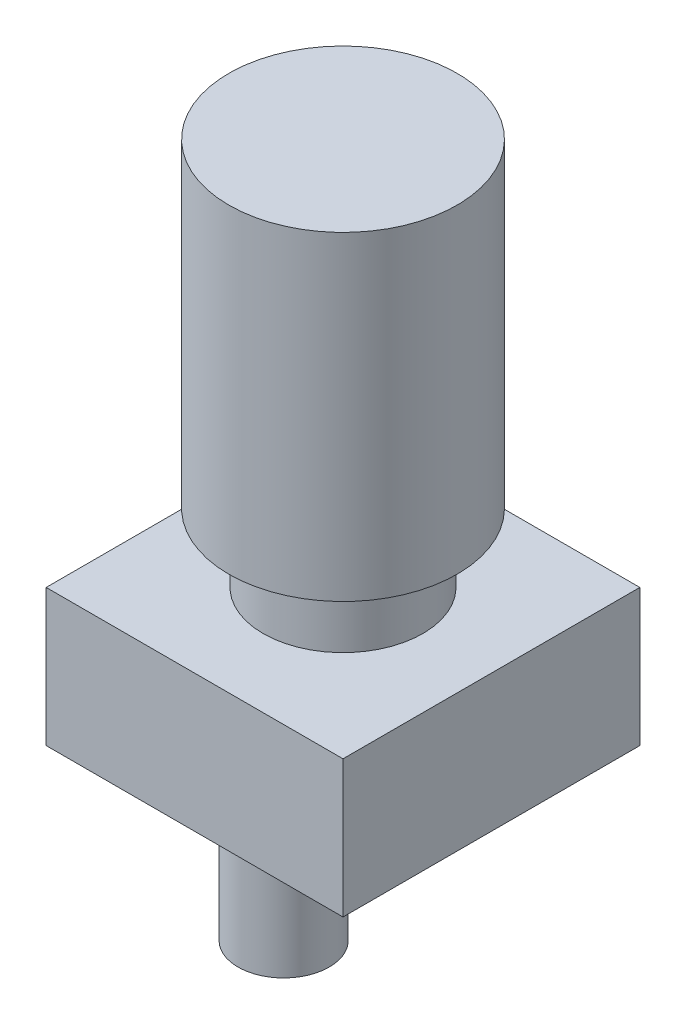
SolidWorks part; units mm, degrees
ref_plane "Front Plane" through (0, 0, 0) normal (0, 0, 1) x (1, 0, 0)
ref_plane "Top Plane" through (0, 0, 0) normal (0, 1, 0) x (1, 0, 0)
ref_plane "Right Plane" through (0, 0, 0) normal (1, 0, 0) x (0, 0, -1)
sketch "Sketch1" plane through (0, 0, 0) normal (0, 1, 0) x (1, 0, 0)
  line L0 (32.5, 32.5) -> (-32.5, -32.5) construction
  line L1 (-32.5, 32.5) -> (32.5, 32.5)
  line L2 (-32.5, 32.5) -> (-32.5, -32.5)
  line L3 (-32.5, -32.5) -> (32.5, -32.5)
  line L4 (32.5, 32.5) -> (32.5, -32.5)
  line L5 (-32.5, 32.5) -> (32.5, -32.5) construction
  dimension "D1" = 65
extrude "Boss-Extrude1" add sketch "Sketch1" along normal blind 30
sketch "Sketch3" plane through (0, 30, 0) normal (0, 1, 0) x (1, 0, 0)
  circle A0 centre (0, 0) radius 17.5
extrude "Boss-Extrude2" add sketch "Sketch3" along normal blind 15
sketch "Sketch4" plane through (0, 45, 0) normal (0, 1, 0) x (1, 0, 0)
  circle A0 centre (0, 0) radius 25
extrude "Boss-Extrude3" add sketch "Sketch4" along normal blind 70
sketch "Sketch5" plane through (0, 0, 0) normal (0, -1, 0) x (1, 0, 0)
  line L0 (32.5, -32.5) -> (-32.5, -32.5) construction
  line L2 (-32.5, -32.5) -> (-32.5, 32.5) construction
  circle A0 centre (-12.5, 0.5) radius 7.5
  dimension "D1" = 33
  dimension "D2" = 20
extrude "Boss-Extrude4" add sketch "Sketch5" along normal blind 3
sketch "Sketch6" plane through (0, -3, 0) normal (0, -1, 0) x (1, 0, 0)
  circle A0 centre (-12.5, 0.5) radius 4
extrude "Boss-Extrude5" add sketch "Sketch6" along normal blind 10
sketch "Sketch7" plane through (0, -13, 0) normal (0, -1, 0) x (1, 0, 0)
  circle A0 centre (-12.5, 0.5) radius 10
extrude "Boss-Extrude6" add sketch "Sketch7" along normal blind 30
sketch "Sketch8" plane through (0, -43, 0) normal (0, -1, 0) x (1, 0, 0)
  line L0 (-17.7339, 3.1069) -> (-7.1406, 3.1069)
  arc A0 (-17.7339, 3.1069) -> (-7.1406, 3.1069) centre (-12.4373, 2.3243) ccw
extrude "Cut-Extrude1" cut sketch "Sketch8" against normal blind 22.38
